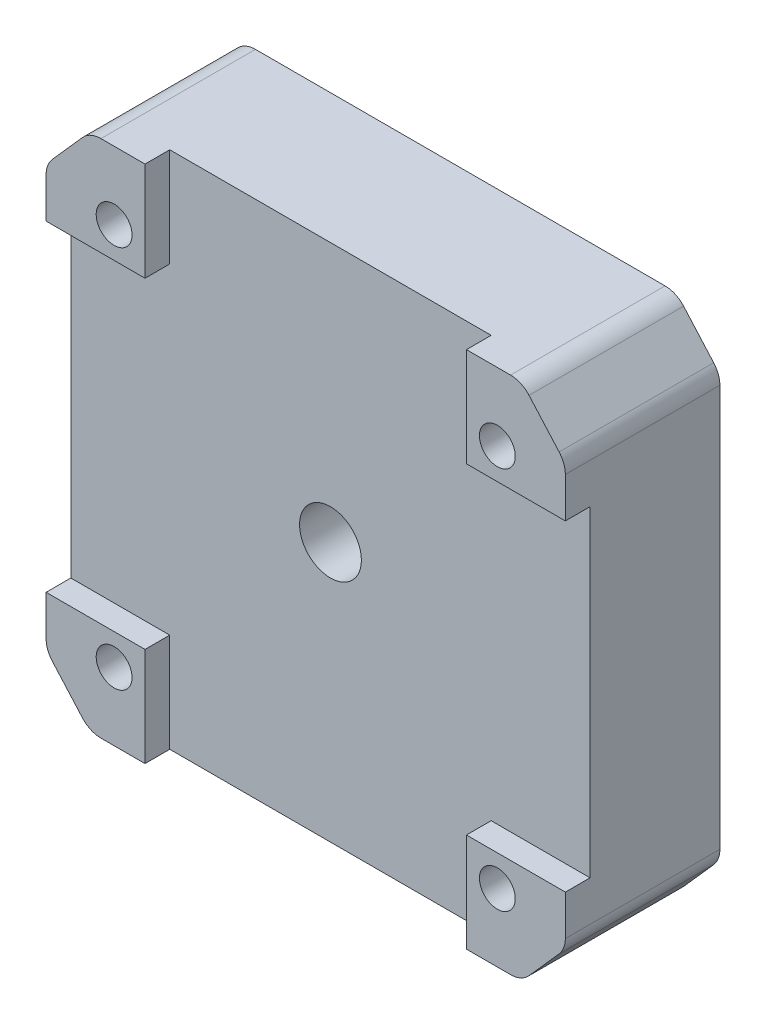
SolidWorks part; units mm, degrees
material "Alumina"
ref_plane "Front" through (0, 0, 0) normal (0, 0, 1) x (1, 0, 0)
ref_plane "Top" through (0, 0, 0) normal (0, 1, 0) x (1, 0, 0)
ref_plane "Right" through (0, 0, 0) normal (1, 0, 0) x (0, 0, -1)
sketch "Sketch1" plane through (0, 0, 0) normal (0, 0, 1) x (1, 0, 0)
  line L0 (-17.4657, 21) -> (-21, 17.0129)
  line L1 (-17.4657, -21) -> (17.4657, -21)
  line L2 (-21, -17.0129) -> (-21, 17.0129)
  line L3 (-17.4657, 21) -> (17.4657, 21)
  line L4 (21, -17.0129) -> (21, 17.0129)
  line L5 (19.2328, 19.0064) -> (-19.2328, -19.0064) construction
  line L6 (-19.2328, 19.0064) -> (19.2328, -19.0064) construction
  line L7 (0, 21) -> (0, -21) construction
  line L8 (-21, 0) -> (21, 0) construction
  line L9 (17.4657, 21) -> (21, 17.0129)
  line L10 (17.4657, -21) -> (21, -17.0129)
  line L11 (-17.4657, -21) -> (-21, -17.0129)
  point P0 (0, 0)
  dimension "D1" = 42
  dimension "D2" = 54
  dimension "D3" = 42
  dimension "D4" = 5.3281
extrude "Boss-Extrude1" add sketch "Sketch1" along normal blind 12.5
sketch "Sketch2" plane through (21, 0, 0) normal (1, 0, 0) x (0, 0, -1)
  line L0 (-12.5, -17.0129) -> (-12.5, 17.0129) construction
  line L1 (-12.5, 13) -> (-10.5, 13)
  line L2 (-12.5, 13) -> (-12.5, -13)
  line L3 (-12.5, -13) -> (-10.5, -13)
  line L4 (-10.5, 13) -> (-10.5, -13)
  line L7 (0, 0) -> (-12.5, 0) construction
  line L8 (0, -17.0129) -> (0, 17.0129) construction
  dimension "D1" = 26
  dimension "D3" = 2
extrude "Cut-Extrude1" cut sketch "Sketch2" against normal through all
sketch "Sketch3" plane through (0, -21, 0) normal (0, -1, 0) x (1, 0, 0)
  line L0 (-17.4657, 12.5) -> (17.4657, 12.5) construction
  line L1 (-13, 12.5) -> (13, 12.5)
  line L2 (-13, 12.5) -> (-13, 10.5)
  line L3 (-13, 10.5) -> (13, 10.5)
  line L4 (13, 12.5) -> (13, 10.5)
  line L7 (0, 0) -> (0, 12.5) construction
  line L8 (-17.4657, 0) -> (17.4657, 0) construction
  dimension "D1" = 2
  dimension "D2" = 26
extrude "Cut-Extrude2" cut sketch "Sketch3" against normal through all
sketch "Sketch4" plane through (0, 0, 0) normal (0, 0, -1) x (-1, 0, 0)
  circle A0 centre (0, 0) radius 3.25
  dimension "D1" = 6.5
extrude "Cut-Extrude3" cut sketch "Sketch4" against normal blind 3
sketch "Sketch5" plane through (0, 0, 10.5) normal (0, 0, 1) x (1, 0, 0)
  circle A0 centre (0, 0) radius 2.5
  dimension "D1" = 5
extrude "Cut-Extrude4" cut sketch "Sketch5" against normal through all
hole_wizard "CBORE for M2.5 Pan Head Machine Screw1" positions "Sketch7" profile "Sketch6" counterbore size "M2.5" standard "ANSI Metric" end condition through all
sketch "Sketch7" plane through (0, 0, 0) normal (0, 0, -1) x (-1, 0, 0)
  line L0 (0, 0) -> (0, 21) construction
  line L1 (-17.4657, 21) -> (17.4657, 21) construction
  line L3 (0, 0) -> (21, 0) construction
  line L4 (21, 17.0129) -> (21, -17.0129) construction
  point P0 (-15.5, 15.5)
  point P8 (15.5, 15.5)
  point P16 (15.5, -15.5)
  point P17 (-15.5, -15.5)
  dimension "D1" = 31
  dimension "D2" = 31
sketch "Sketch6" plane through (15.5, 15.5, 0) normal (1, 0, 0) x (0, 1, 0)
  line L0 (0, 0) -> (0, 12.5)
  line L1 (0, 12.5) -> (1.45, 12.5)
  line L3 (1.45, 12.5) -> (1.45, 2.1)
  line L4 (1.45, 2.1) -> (3, 2.1)
  line L5 (3, 2.1) -> (3, 0)
  line L7 (3, 0) -> (0, 0)
  line L11 (0, -6.35) -> (0, 107.95) construction
  dimension "Thru Hole Dia." = 2.9
  dimension "Thru Hole Depth" = 12.5
  dimension "C'Bore Dia." = 6
  dimension "C'Bore Depth" = 2.1
fillet "Fillet1" radius 2 8 edges at (-21, -17.0129, 6.25) (-17.4657, -21, 6.25) (17.4657, -21, 6.25) (21, -17.0129, 6.25) (21, 17.0129, 6.25) (17.4657, 21, 6.25) (-21, 17.0129, 6.25) (-17.4657, 21, 6.25)
